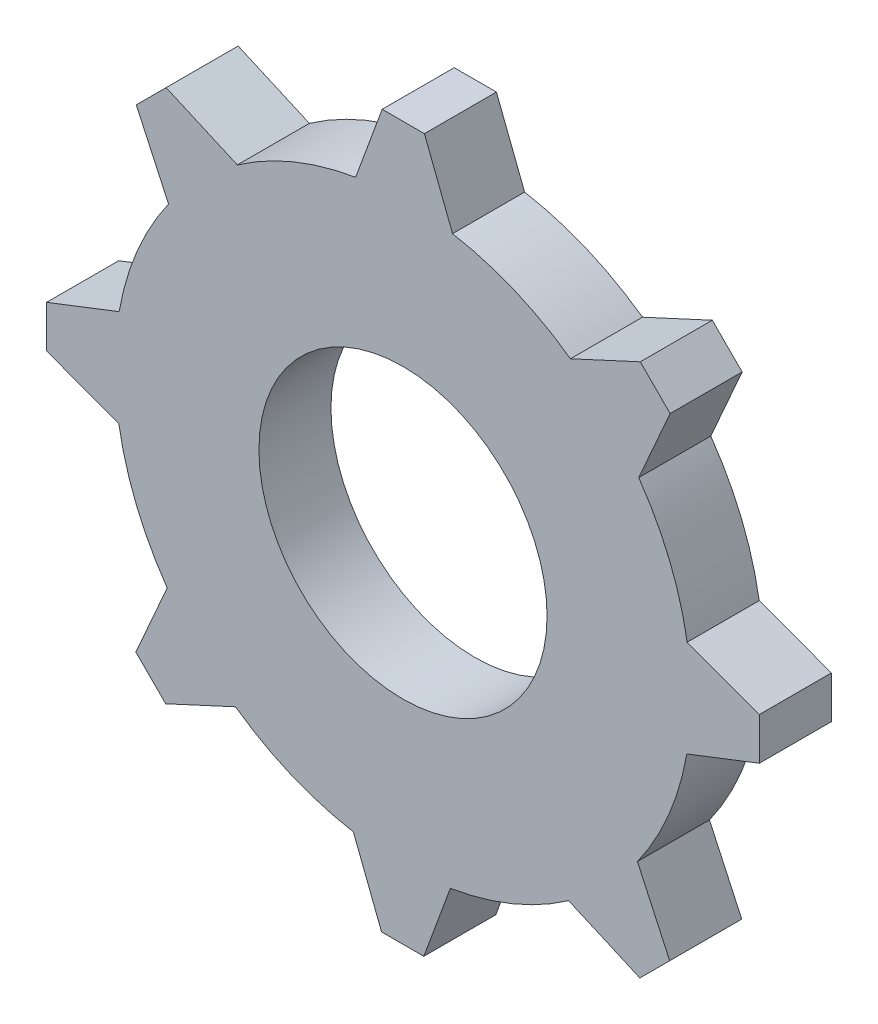
SolidWorks part; units mm, degrees
ref_plane "Alzado" through (0, 0, 0) normal (0, 0, 1) x (1, 0, 0)
ref_plane "Planta" through (0, 0, 0) normal (0, 1, 0) x (1, 0, 0)
ref_plane "Vista lateral" through (0, 0, 0) normal (1, 0, 0) x (0, 0, -1)
sketch "Croquis1" plane through (0, 0, 0) normal (0, 0, 1) x (1, 0, 0)
  circle A0 centre (0, 0) radius 8
  circle A1 centre (0, 0) radius 4
extrude "Saliente-Extruir5" add sketch "Croquis1" along normal blind 2
sketch "Croquis5" plane through (0, 0, 0) normal (0, 0, 1) x (1, 0, 0)
  line L1 (0.0093, 9.8945) -> (-0.5778, 9.8945)
  line L2 (-0.5778, 9.8945) -> (-1.3147, 7.8912)
  line L3 (-1.3147, 7.8912) -> (-1.3147, 7.5651)
  line L4 (-1.3147, 7.5651) -> (1.3768, 7.5651)
  line L5 (1.3768, 7.5651) -> (1.3768, 7.8806)
  line L6 (1.3768, 7.8806) -> (0.5945, 9.8945)
  line L7 (0.5945, 9.8945) -> (0.0093, 9.8945)
  circle A0 centre (0, 0) radius 8 construction
extrude "Saliente-Extruir7" add sketch "Croquis5" along normal blind 2
pattern_circular "MatrizC5" count 8 over 360 about axis through (0, 0, 0) along (0, 0, 1) of "Saliente-Extruir7"
